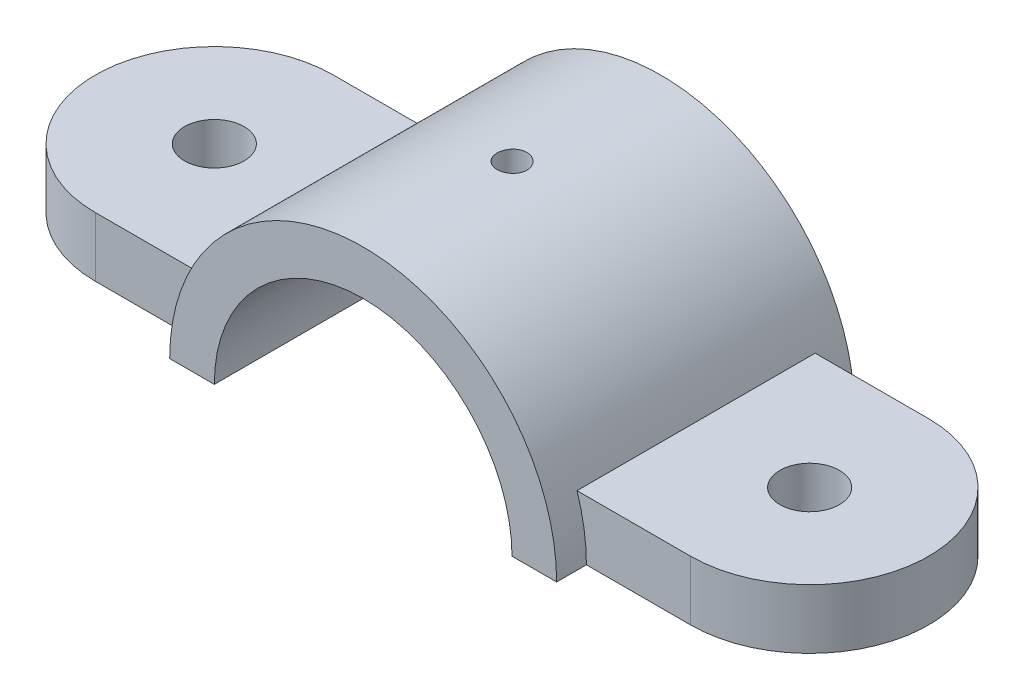
SolidWorks part; units mm, degrees
ref_plane "Front Plane" through (0, 0, 0) normal (0, 0, 1) x (1, 0, 0)
ref_plane "Top Plane" through (0, 0, 0) normal (0, 1, 0) x (1, 0, 0)
ref_plane "Right Plane" through (0, 0, 0) normal (1, 0, 0) x (0, 0, -1)
sketch "Sketch5" plane through (0, 0, 0) normal (0, 1, 0) x (1, 0, 0)
  line L0 (-63.5, 0) -> (63.5, 0) construction
  line L1 (-63.5, 25.4) -> (63.5, 25.4)
  line L2 (-63.5, -25.4) -> (63.5, -25.4)
  arc A0 (-63.5, 25.4) -> (-63.5, -25.4) centre (-63.5, 0) ccw
  arc A1 (63.5, -25.4) -> (63.5, 25.4) centre (63.5, 0) ccw
  circle A2 centre (-63.5, 0) radius 6.35
  circle A3 centre (63.5, 0) radius 6.35
  point P3 (0, 0)
  dimension "D2" = 25.4
  dimension "D3" = 12.7
  dimension "D1" = 127
extrude "Boss-Extrude2" add sketch "Sketch5" along normal blind 12.7
sketch "Sketch6" plane through (0, 0, 0) normal (0, 0, 1) x (1, 0, 0)
  line L0 (-63.5, 0) -> (-63.5, 39.9621) construction
  line L1 (-63.5, 39.9621) -> (63.5, 39.9621) construction
  line L2 (63.5, 39.9621) -> (63.5, 0) construction
  line L3 (63.5, 0) -> (-63.5, 0) construction
  line L4 (-41.275, 0) -> (41.275, 0)
  line L5 (-63.5, 0) -> (63.5, 0) construction
  arc A0 (-41.275, 0) -> (41.275, 0) centre (0, 0) cw
  point P4 (-61.0214, 0)
  point P6 (0, 0)
  point P11 (-63.5756, 0)
  point P12 (0, 0)
  point P13 (-63.5669, 0)
  point P14 (-59.6629, 0)
  point P17 (-63.5, 0)
  dimension "D1" = 41.275
  dimension "D2" = 127
  dimension "D3" = 82.55
  dimension "D4" = 22.225
extrude "Boss-Extrude3" add sketch "Sketch6" along normal mid plane 63.5
sketch "Sketch7" plane through (0, 0, 31.75) normal (0, 0, 1) x (1, 0, 0)
  line L0 (-41.275, 0) -> (41.275, 0) construction
  line L1 (-31.75, 0) -> (31.75, 0)
  arc A0 (-31.75, 0) -> (31.75, 0) centre (0, 0) cw
  dimension "D1" = 31.75
extrude "Cut-Extrude1" cut sketch "Sketch7" against normal blind 63.5
sketch "Sketch9" plane through (0, 0, 0) normal (0, 0, 1) x (1, 0, 0)
  line L0 (0, 0) -> (0, 41.275) construction
  arc A0 (41.275, 0) -> (-41.275, 0) centre (0, 0) ccw construction
  point P6 (0, 0)
  point P7 (0, 0)
ref_plane "Plane1" through (0, 41.275, 0) normal (0, 1, 0) x (1, 0, 0)
sketch "Sketch10" plane through (0, 41.275, 0) normal (0, 1, 0) x (1, 0, 0)
  circle A0 centre (0, 0) radius 3.175
extrude "Cut-Extrude2" cut sketch "Sketch10" against normal blind 63.5
